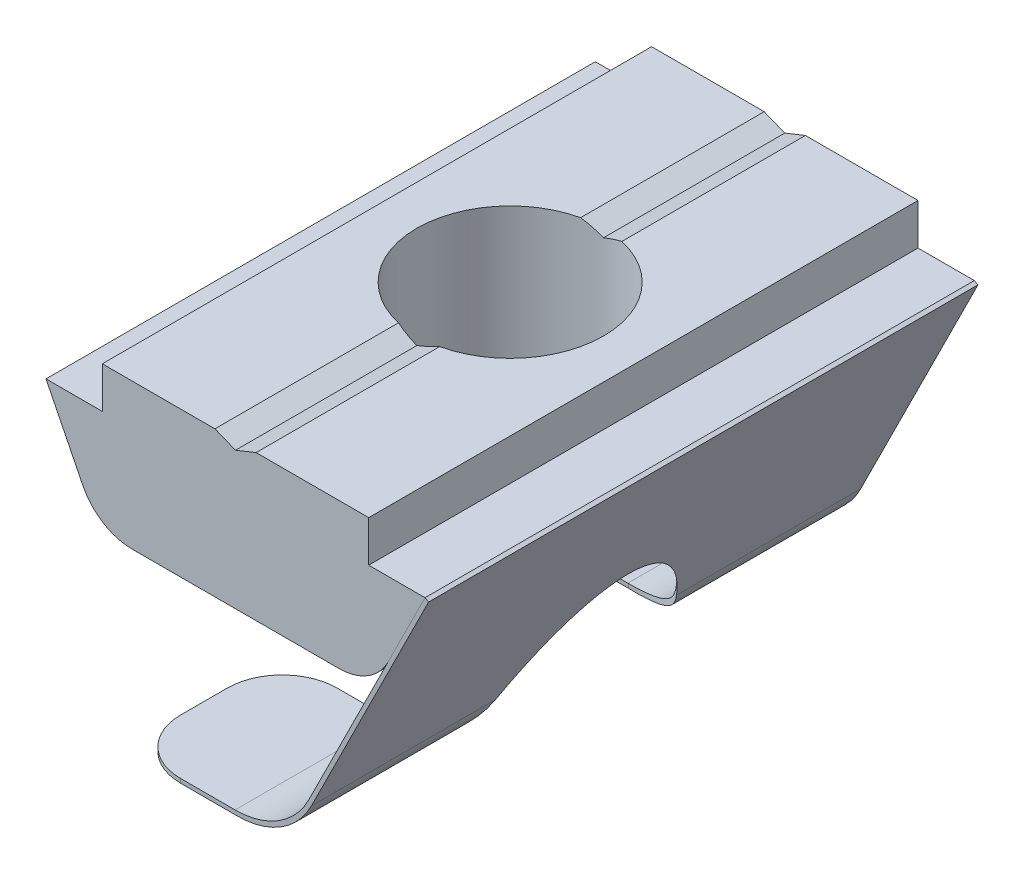
SolidWorks part; units mm, degrees
ref_plane "Спереди" through (0, 0, 0) normal (0, 0, 1) x (1, 0, 0)
ref_plane "Сверху" through (0, 0, 0) normal (0, 1, 0) x (1, 0, 0)
ref_plane "Справа" through (0, 0, 0) normal (1, 0, 0) x (0, 0, -1)
sketch "Эскиз1" plane through (0, 0, 0) normal (0, 0, 1) x (1, 0, 0)
  line L0 (0, 0) -> (0.75, 0.3)
  line L5 (3.7678, -5) -> (-3.7678, -5)
  line L6 (0, 0) -> (0, -5) construction
  line L17 (6.9, -1.2) -> (5.5576, -3.8924)
  line L18 (0.75, 0.3) -> (4.85, 0.3)
  line L19 (4.85, 0.3) -> (4.85, -1.2)
  line L20 (4.85, -1.2) -> (6.9, -1.2)
  line L21 (-4.85, -1.2) -> (-6.9, -1.2)
  line L22 (-4.85, 0.3) -> (-4.85, -1.2)
  line L23 (-0.75, 0.3) -> (-4.85, 0.3)
  line L24 (-6.9, -1.2) -> (-5.5576, -3.8924)
  line L25 (0, 0) -> (-0.75, 0.3)
  arc A0 (5.5576, -3.8924) -> (3.7678, -5) centre (3.7678, -3) cw
  arc A1 (-5.5576, -3.8924) -> (-3.7678, -5) centre (-3.7678, -3) ccw
  dimension "D9" = 2
  dimension "D1" = 6.9
  dimension "D2" = 4.85
  dimension "D3" = 1.5
  dimension "D4" = 5.3
  dimension "D5" = 0.3
  dimension "D6" = 26.5
  dimension "D8" = 0.75
extrude "Бобышка-Вытянуть1" add sketch "Эскиз1" along normal mid plane 20
sketch "Эскиз2" plane through (0, 0, 0) normal (0, 0, 1) x (1, 0, 0)
  line L0 (6.9, -1.2) -> (2.6677, -9.6886)
  line L2 (0.0758, -11.5) -> (-4, -11.5)
  line L3 (4.85, 0.3) -> (0.75, 0.3) construction
  line L4 (7.0342, -1.2669) -> (2.7606, -9.8386)
  line L5 (-0.0171, -11.35) -> (-4, -11.35)
  line L6 (3.4149, -11.35) -> (-4, -11.35) construction
  line L7 (3.4149, -11.5) -> (-4, -11.5) construction
  line L8 (7.0342, -1.2669) -> (-0.577, -16.5326) construction
  line L9 (6.9, -1.2) -> (-0.7112, -16.4657) construction
  line L10 (-4, -11.35) -> (-4, -11.5)
  line L11 (6.9, -1.2) -> (7.0342, -1.2669)
  arc A0 (0.0758, -11.5) -> (2.7606, -9.8386) centre (0.0758, -8.5) ccw
  arc A1 (2.6677, -9.6886) -> (-0.0171, -11.35) centre (-0.0171, -8.35) cw
  dimension "D5" = 3
  dimension "D1" = 10.9
  dimension "D2" = 11.8
  dimension "D3" = 0.15
  dimension "D4" = 0.15
extrude "Бобышка-Вытянуть2" add sketch "Эскиз2" along normal mid plane 20 separate body
sketch "Эскиз3" plane through (0, -5, 0) normal (0, -1, 0) x (1, 0, 0)
  line L0 (0, 4.3) -> (-5.5576, 4.3)
  line L1 (-5.5576, 10) -> (-5.5576, -10) construction
  line L2 (-5.5576, 4.3) -> (-5.5576, -4.3)
  line L3 (-5.5576, -4.3) -> (0, -4.3)
  arc A0 (0, -4.3) -> (0, 4.3) centre (0, 0) ccw
  dimension "D1" = 8.6
extrude "Вырез-Вытянуть1" cut sketch "Эскиз3" along normal blind 20
fillet "Скругление1" radius 2 4 edges at (-4, -11.425, 10) (-4, -11.425, 4.3) (-4, -11.425, -4.3) (-4, -11.425, -10)
hole_wizard "Отверстие обработанное метчиком M81" positions "Трехмерный эскиз1" profile "Эскиз4" tap size "M8" standard "DIN" end condition through all
sketch3d "Трехмерный эскиз1"
  point P0 (0, 0.3, 0)
  dimension "D1" = 10
  dimension "D2" = 4.85
sketch "Эскиз4" plane through (0, 0.3, 0) normal (1, 0, 0) x (0, 0, 1)
  line L0 (0, 0) -> (0, 11.8)
  line L1 (0, 11.8) -> (3.4, 11.8)
  line L2 (3.4, 11.8) -> (3.4, 0)
  line L5 (3.4, 0) -> (0, 0)
  line L11 (0, -6.35) -> (0, 107.95) construction
  dimension "Диаметр проходного сверла" = 6.8
  dimension "Глубина проходного сверла" = 11.8
cosmetic thread "Отверстие резьбы1"
